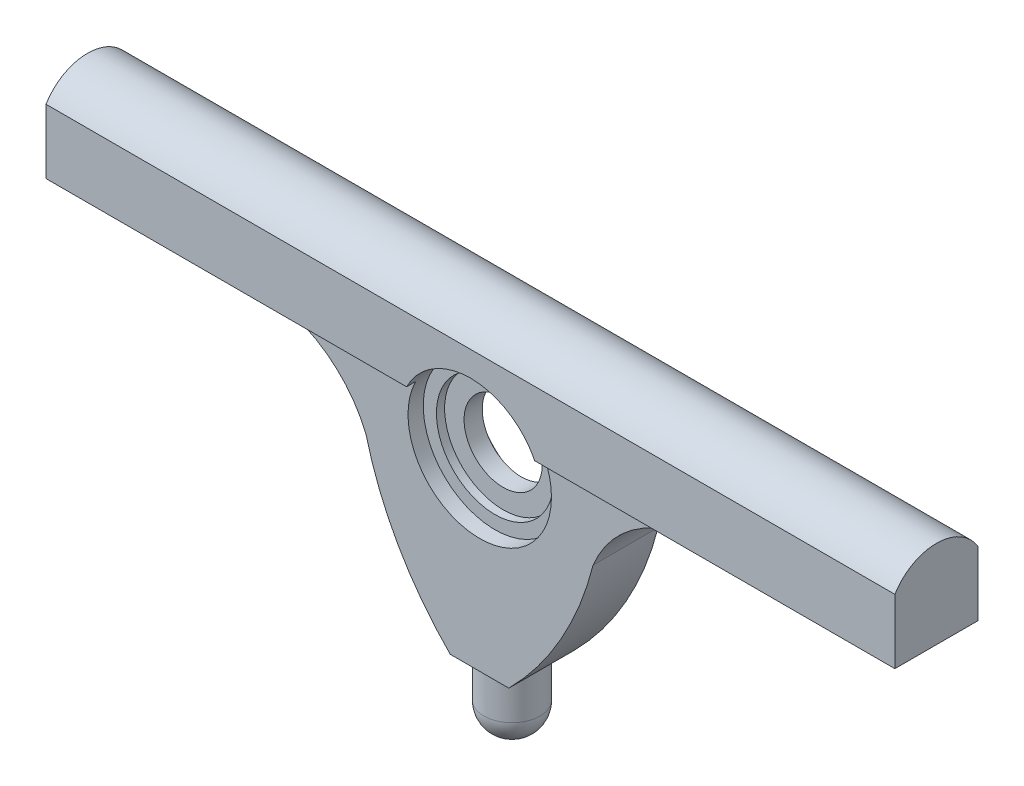
SolidWorks part; units mm, degrees
ref_plane "Front Plane" through (0, 0, 0) normal (0, 0, 1) x (1, 0, 0)
ref_plane "Top Plane" through (0, 0, 0) normal (0, 1, 0) x (1, 0, 0)
ref_plane "Right Plane" through (0, 0, 0) normal (1, 0, 0) x (0, 0, -1)
sketch "Sketch1" plane through (0, 0, 0) normal (1, 0, 0) x (0, 0, -1)
  line L1 (-9.017, -6.985) -> (9.017, -6.985)
  line L2 (-9.017, -6.985) -> (-9.017, 6.985)
  line L4 (9.017, -6.985) -> (9.017, 6.985)
  line L5 (-9.017, -6.985) -> (9.017, 6.985) construction
  line L6 (-9.017, 6.985) -> (9.017, -6.985) construction
  arc A0 (-9.017, 6.985) -> (9.017, 6.985) centre (0, 1.5224) cw
  point P0 (0, 0)
  point P7 (0, 12.065)
  dimension "D1" = 19.05
  dimension "D2" = 13.97
  dimension "D3" = 18.034
extrude "Boss-Extrude1" add sketch "Sketch1" along normal mid plane 184.15
sketch3d "3DSketch1"
  line L0 (0, -6.985, 0) -> (0, -54.483, 0) construction
  line L1 (-24.638, -22.225, 0) -> (0, -22.225, 0) construction
  line L2 (6.35, -54.483, 0) -> (-6.35, -54.483, 0)
  line L3 (-43.18, -6.985, 0) -> (43.18, -6.985, 0)
  arc A0 (-43.18, -6.985, 0) -> (-24.638, -22.225, 0) centre (-48.1235, -31.8993, 0) cw
  arc A1 (-24.638, -22.225, 0) -> (-6.35, -54.483, 0) centre (43.0905, -5.1407, 0) cw
  arc A2 (24.638, -22.225, 0) -> (6.35, -54.483, 0) centre (-43.0905, -5.1407, 0) ccw
  arc A3 (43.18, -6.985, 0) -> (24.638, -22.225, 0) centre (48.1235, -31.8993, 0) ccw
  point P7 (-48.1235, -31.8993, -25.4)
  point P10 (43.0905, -5.1407, 69.85)
  point P15 (-43.0905, -5.1407, -69.85)
  point P18 (48.1235, -31.8993, 25.4)
  dimension "D5" = 25.4
  dimension "D6" = 69.85
  dimension "D1" = 24.638
  dimension "D2" = 47.498
  dimension "D3" = 15.24
  dimension "D4" = 43.18
  dimension "D7" = 6.35
extrude "Boss-Extrude2" add sketch "3DSketch1" along direction (0, 0, -1) on the side of the normal mid plane 14.097
ref_plane "Plane1" through (0, 0, 0) normal (0, 0, 1) x (1, 0, 0)
sketch "Sketch8" plane through (0, 0, 0) normal (0, 0, 1) x (1, 0, 0)
  line L0 (0, -69.469) -> (0, -54.483)
  line L1 (-6.35, -54.483) -> (6.35, -54.483) construction
  line L2 (0, -54.483) -> (6.096, -54.483)
  line L3 (6.096, -54.483) -> (6.096, -63.373)
  line L4 (0, -47.1342) -> (0, -77.1544) construction
  arc A0 (6.096, -63.373) -> (0, -69.469) centre (0, -63.373) cw
  dimension "D1" = 8.89
  dimension "D2" = 6.096
revolve "Revolve2" add sketch "Sketch8" angle 360 about L4
sketch "Sketch9" plane through (0, 0, 7.0485) normal (0, 0, 1) x (1, 0, 0)
  circle A0 centre (0.0506, -13.9773) radius 4.6736
ref_plane "Plane2" through (0, -13.9773, 0) normal (0, -1, 0) x (-1, 0, 0)
sketch "Sketch10" plane through (0, -13.9773, 0) normal (0, -1, 0) x (-1, 0, 0)
  line L0 (-0.0506, -55.7699) -> (-0.0506, 64.4216) construction
  line L1 (-0.0506, -9.017) -> (-0.0506, 9.017)
  line L2 (19.1976, 0) -> (-22.9025, 0) construction
  line L4 (-0.0506, 9.017) -> (-15.6081, 9.017)
  line L5 (-15.6081, 9.017) -> (-15.6081, 3.7465)
  line L6 (-15.6081, 3.7465) -> (-12.7506, 3.7465)
  line L7 (-12.7506, 3.7465) -> (-12.7506, 1.9685)
  line L8 (-12.7506, 1.9685) -> (-8.5342, 1.9685)
  line L9 (-8.5342, 1.9685) -> (-8.5342, -1.9685)
  line L10 (-64.6711, 0) -> (64.6711, 0) construction
  line L12 (-0.0506, -9.017) -> (-15.6081, -9.017)
  line L13 (-15.6081, -9.017) -> (-15.6081, -3.7465)
  line L14 (-15.6081, -3.7465) -> (-12.7506, -3.7465)
  line L15 (-12.7506, -3.7465) -> (-12.7506, -1.9685)
  line L16 (-12.7506, -1.9685) -> (-8.5342, -1.9685)
  line L17 (-92.075, 9.017) -> (92.075, 9.017) construction
  point P5 (-0.0506, 0)
  point P23 (-8.5342, 0)
  dimension "D3" = 15.5575
  dimension "D4" = 12.7
  dimension "D5" = 8.4836
revolve "Cut-Revolve1" cut sketch "Sketch10" angle 360 about L0
